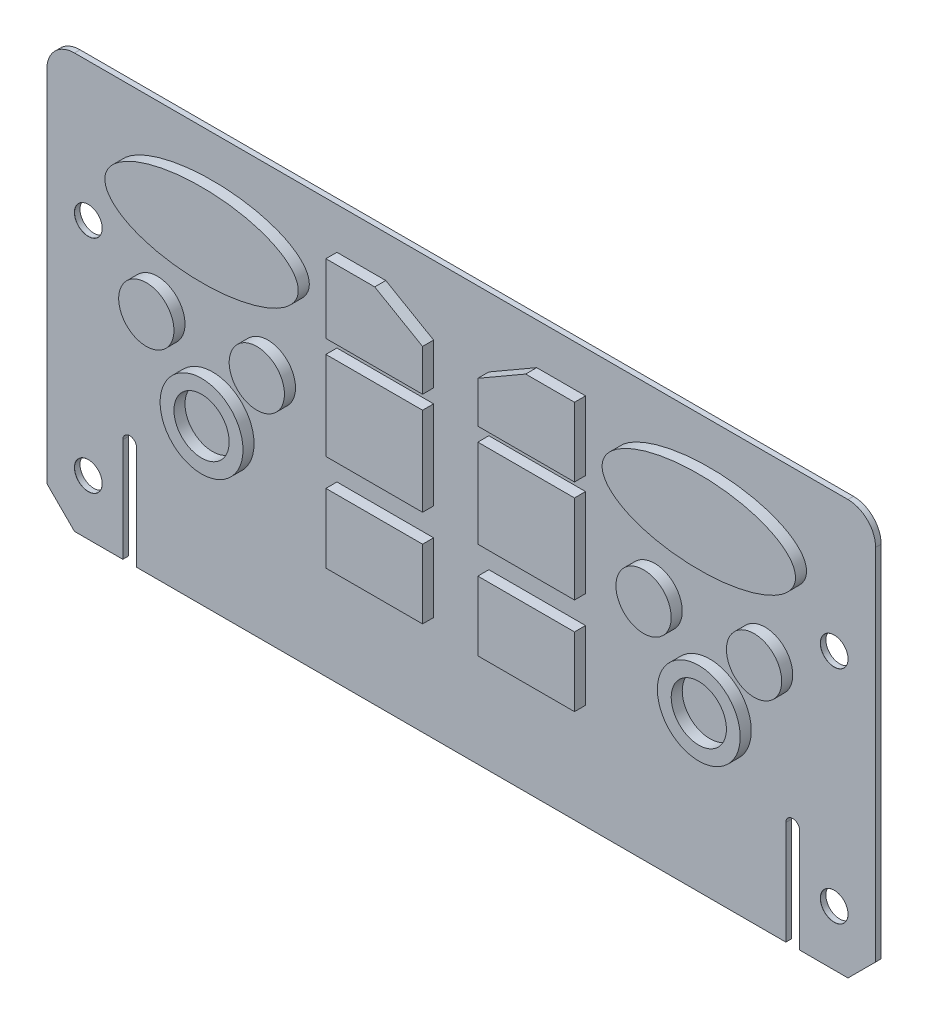
SolidWorks part; units mm, degrees
ref_plane "Front Plane" through (0, 0, 0) normal (0, 0, 1) x (1, 0, 0)
ref_plane "Top Plane" through (0, 0, 0) normal (0, 1, 0) x (1, 0, 0)
ref_plane "Right Plane" through (0, 0, 0) normal (1, 0, 0) x (0, 0, -1)
sketch "Sketch1" plane through (0, 0, 0) normal (0, 0, 1) x (1, 0, 0)
  line L0 (-300, 150) -> (-300, 0)
  line L1 (-300, 0) -> (0, 0)
  line L2 (0, 0) -> (0, 150)
  line L3 (0, 150) -> (-300, 150)
  dimension "D1" = 300
  dimension "D2" = 150
extrude "PCB Base" add sketch "Sketch1" along normal mid plane 2
sketch "Sketch2" plane through (0, 0, 1) normal (0, 0, 1) x (1, 0, 0)
  line L0 (-300, 0) -> (0, 0) construction
  line L1 (-300, 150) -> (-300, 0) construction
  line L2 (0, 0) -> (0, 150) construction
  line L3 (-195, 38) -> (-160, 38)
  line L4 (-195, 38) -> (-195, 63)
  line L5 (-195, 63) -> (-160, 63)
  line L6 (-160, 38) -> (-160, 63)
  line L7 (-195, 73) -> (-160, 73)
  line L8 (-195, 73) -> (-195, 105)
  line L9 (-195, 105) -> (-160, 105)
  line L10 (-160, 73) -> (-160, 105)
  line L11 (-195, 110) -> (-160, 110)
  line L12 (-195, 110) -> (-195, 135)
  line L13 (-195, 135) -> (-177.3205, 135)
  line L14 (-160, 110) -> (-160, 125)
  line L15 (-160, 125) -> (-177.3205, 135)
  line L16 (-150, 150) -> (-150, 0) construction
  line L17 (0, 150) -> (-300, 150) construction
  line L18 (-140, 125) -> (-122.6795, 135)
  line L19 (-140, 110) -> (-140, 125)
  line L20 (-105, 135) -> (-122.6795, 135)
  line L21 (-105, 110) -> (-105, 135)
  line L22 (-105, 110) -> (-140, 110)
  line L23 (-140, 73) -> (-140, 105)
  line L24 (-105, 105) -> (-140, 105)
  line L25 (-105, 73) -> (-105, 105)
  line L26 (-105, 73) -> (-140, 73)
  line L27 (-140, 38) -> (-140, 63)
  line L28 (-105, 63) -> (-140, 63)
  line L29 (-105, 38) -> (-105, 63)
  line L30 (-105, 38) -> (-140, 38)
  circle A0 centre (-260, 85) radius 10
  circle A1 centre (-220, 85) radius 10
  circle A2 centre (-240, 60) radius 15
  circle A3 centre (-240, 60) radius 10
  circle A4 centre (-60, 60) radius 10
  circle A5 centre (-60, 60) radius 15
  circle A6 centre (-80, 85) radius 10
  circle A7 centre (-40, 85) radius 10
  ellipse E0 centre (-240, 120) end of major axis (-205, 120) minor radius 15
  ellipse E1 centre (-60, 120) end of major axis (-25, 120) minor radius 15
  dimension "D1" = 20
  dimension "D5" = 30
  dimension "D8" = 5
  dimension "D2" = 85
  dimension "D3" = 40
  dimension "D4" = 40
  dimension "D6" = 60
  dimension "D7" = 60
  dimension "D9" = 60
  dimension "D10" = 120
  dimension "D11" = 70
  dimension "D12" = 30
  dimension "D13" = 38
  dimension "D14" = 25
  dimension "D15" = 73
  dimension "D16" = 110
  dimension "D17" = 32
  dimension "D18" = 135
  dimension "D19" = 195
  dimension "D20" = 160
  dimension "D21" = 125
  dimension "D22" = 120
extrude "PCB Chips" add sketch "Sketch2" along normal blind 4
mirror "Mirror Chips" about plane through (0, 0, 0) normal (0, 0, 1) of "PCB Chips"
sketch "Sketch3" plane through (0, 0, 1) normal (0, 0, 1) x (1, 0, 0)
  line L0 (-272.5, 37.5) -> (-272.5, 0)
  line L1 (-300, 0) -> (0, 0) construction
  line L2 (-272.5, 0) -> (-267.5, 0)
  line L3 (-267.5, 0) -> (-267.5, 37.5)
  line L4 (-300, 150) -> (-300, 0) construction
  line L5 (-30, 0) -> (-30, 37.5) construction
  line L6 (-32.5, 0) -> (-32.5, 37.5)
  line L7 (-27.5, 0) -> (-27.5, 37.5)
  line L8 (-150, 150) -> (-150, 0) construction
  line L9 (0, 150) -> (-300, 150) construction
  arc A0 (-272.5, 37.5) -> (-267.5, 37.5) centre (-270, 37.5) cw
  arc A1 (-32.5, 0) -> (-27.5, 0) centre (-30, 0) ccw
  arc A2 (-27.5, 37.5) -> (-32.5, 37.5) centre (-30, 37.5) ccw
  point P7 (-30, 18.75)
  dimension "D4" = 2.5
  dimension "D1" = 5
  dimension "D2" = 27.5
  dimension "D3" = 40
  dimension "D5" = 5
extrude "Slot Cut" cut sketch "Sketch3" against normal blind 10
hole_wizard "Ø10.0mm Dowel Hole1" positions "Sketch4" profile "Sketch5" hole size "Ø10.0" standard "ANSI Metric"
sketch "Sketch4" plane through (0, 0, 1) normal (0, 0, 1) x (1, 0, 0)
  line L0 (-300, 0) -> (-272.5, 0) construction
  line L1 (-300, 150) -> (-300, 0) construction
  line L2 (-150, 150) -> (-150, 0) construction
  line L3 (0, 150) -> (-300, 150) construction
  line L4 (-267.5, 0) -> (-32.5, 0) construction
  point P0 (-285, 100)
  point P2 (-285, 20)
  point P4 (-15, 20)
  point P6 (-15, 100)
  point P28 (0, 0)
  dimension "D1" = 20
  dimension "D2" = 100
  dimension "D3" = 15
sketch "Sketch5" plane through (-285, 100, 1) normal (1, 0, 0) x (0, -1, 0)
  line L0 (0, 0) -> (0, 13.0043)
  line L1 (0, 13.0043) -> (5, 10)
  line L2 (5, 10) -> (5, 0.025)
  line L3 (5, 0.025) -> (5.025, 0)
  line L5 (5.025, 0) -> (0, 0)
  line L6 (-5, 0.025) -> (-5.025, 0) construction
  line L10 (0, 13.0043) -> (-5, 10) construction
  line L11 (0, -6.35) -> (0, 107.95) construction
  dimension "Hole Dia." = 10
  dimension "Hole Depth" = 10
  dimension "Near C'Sink Dia." = 10.05
  dimension "Near C'Sink Angle" = 90
  dimension "Drill Angle" = 118
fillet "Fillet1" radius 10 2 edges at (-300, 150, 0) (0, 150, 0)
chamfer "Chamfer1" distance 10 angle 45 2 edges at (-300, 0, 0) (0, 0, 0)
sketch "Sketch7" plane through (0, 0, 1) normal (0, 0, 1) x (1, 0, 0)
  line L0 (-267.5, 0) -> (-32.5, 0) construction
  line L1 (-261, 0) -> (-259, 0)
  line L2 (-261, 0) -> (-261, 25)
  line L3 (-261, 25) -> (-259, 25)
  line L4 (-259, 0) -> (-259, 25)
  line L5 (-267.5, 0) -> (-267.5, 37.5) construction
  dimension "D1" = 6.5
  dimension "D2" = 2
  dimension "D3" = 25
